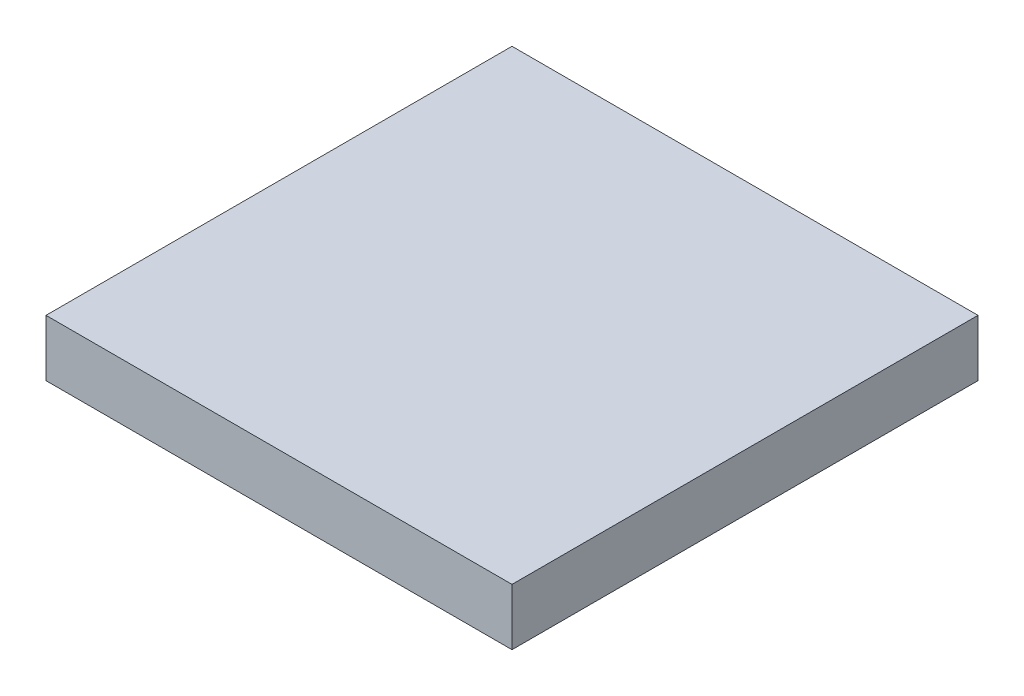
SolidWorks part; units mm, degrees
ref_plane "Front Plane" through (0, 0, 0) normal (0, 0, 1) x (1, 0, 0)
ref_plane "Top Plane" through (0, 0, 0) normal (0, 1, 0) x (1, 0, 0)
ref_plane "Right Plane" through (0, 0, 0) normal (1, 0, 0) x (0, 0, -1)
sketch "Sketch1" plane through (0, 0, 0) normal (0, 1, 0) x (1, 0, 0)
  line L1 (0, 0) -> (7, 0)
  line L2 (0, 0) -> (0, 7)
  line L3 (0, 7) -> (7, 7)
  line L4 (7, 0) -> (7, 7)
  dimension "D1" = 7
  dimension "D2" = 7
extrude "Boss-Extrude1" add sketch "Sketch1" along normal blind 0.85
